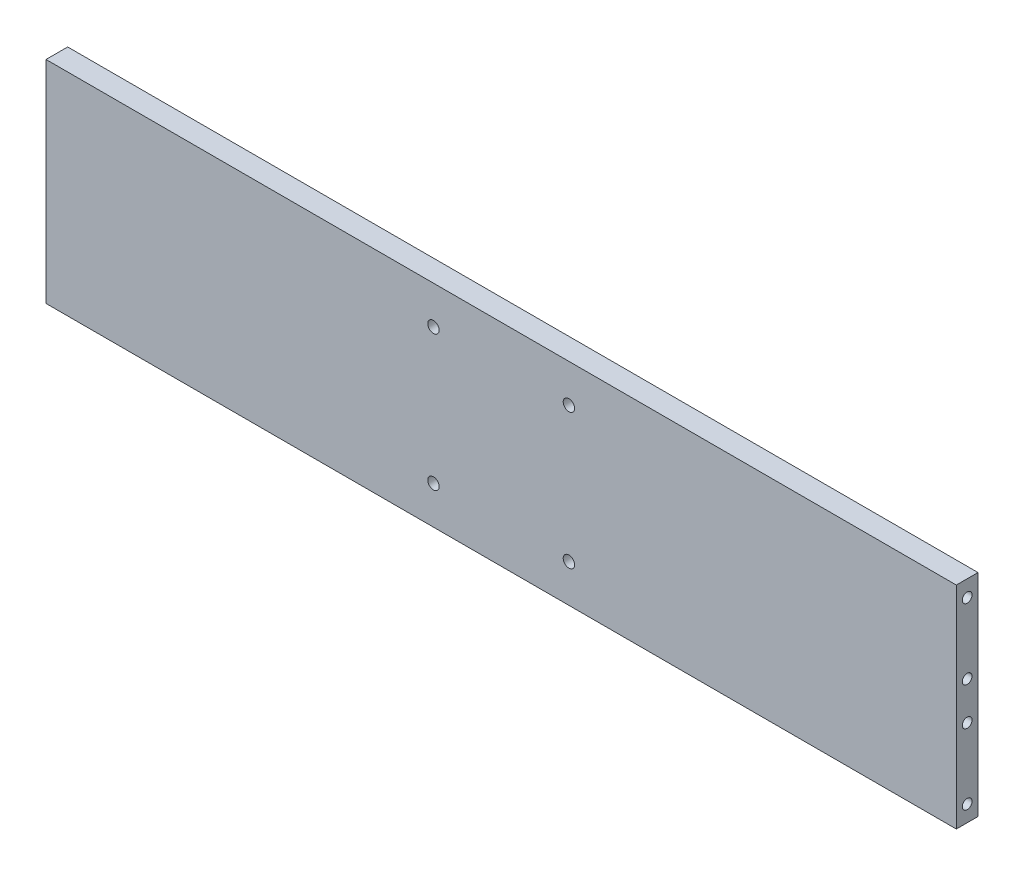
SolidWorks part; units mm, degrees
ref_plane "Front Plane" through (0, 0, 0) normal (0, 0, 1) x (1, 0, 0)
ref_plane "Top Plane" through (0, 0, 0) normal (0, 1, 0) x (1, 0, 0)
ref_plane "Right Plane" through (0, 0, 0) normal (1, 0, 0) x (0, 0, -1)
sketch "Sketch1" plane through (0, 0, 0) normal (0, 0, 1) x (1, 0, 0)
  line L1 (-168, -39) -> (168, -39)
  line L2 (-168, -39) -> (-168, 39)
  line L3 (-168, 39) -> (168, 39)
  line L4 (168, -39) -> (168, 39)
  line L5 (-168, -39) -> (168, 39) construction
  line L6 (-168, 39) -> (168, -39) construction
  line L7 (-25, -25) -> (25, -25) construction
  line L8 (-25, -25) -> (-25, 25) construction
  line L9 (-25, 25) -> (25, 25) construction
  line L10 (25, -25) -> (25, 25) construction
  line L11 (-25, -25) -> (25, 25) construction
  line L12 (-25, 25) -> (25, -25) construction
  circle A0 centre (-25, 25) radius 2.1
  circle A1 centre (25, 25) radius 2.1
  circle A2 centre (25, -25) radius 2.1
  circle A3 centre (-25, -25) radius 2.1
  point P0 (0, 0)
  point P6 (0, 0)
  dimension "D1" = 336
  dimension "D2" = 78
  dimension "D3" = 50
  dimension "D4" = 50
extrude "Boss-Extrude1" add sketch "Sketch1" along normal blind 8
sketch "Sketch2" plane through (168, 0, 0) normal (1, 0, 0) x (0, 0, -1)
  line L0 (-8, 0) -> (0, 0) construction
  line L1 (-8, -39) -> (-8, 39) construction
  line L2 (0, -39) -> (0, 39) construction
  line L3 (-4, 39) -> (-4, 0) construction
  line L4 (-8, 39) -> (0, 39) construction
  circle A0 centre (-4, 33) radius 1.8
  circle A1 centre (-4, 7) radius 1.8
  circle A2 centre (-4, -7) radius 1.8
  circle A3 centre (-4, -33) radius 1.8
  point P14 (-4, 19.5)
  dimension "D1" = 26
  dimension "D2" = 7
extrude "Cut-Extrude1" cut sketch "Sketch2" against normal up to next
